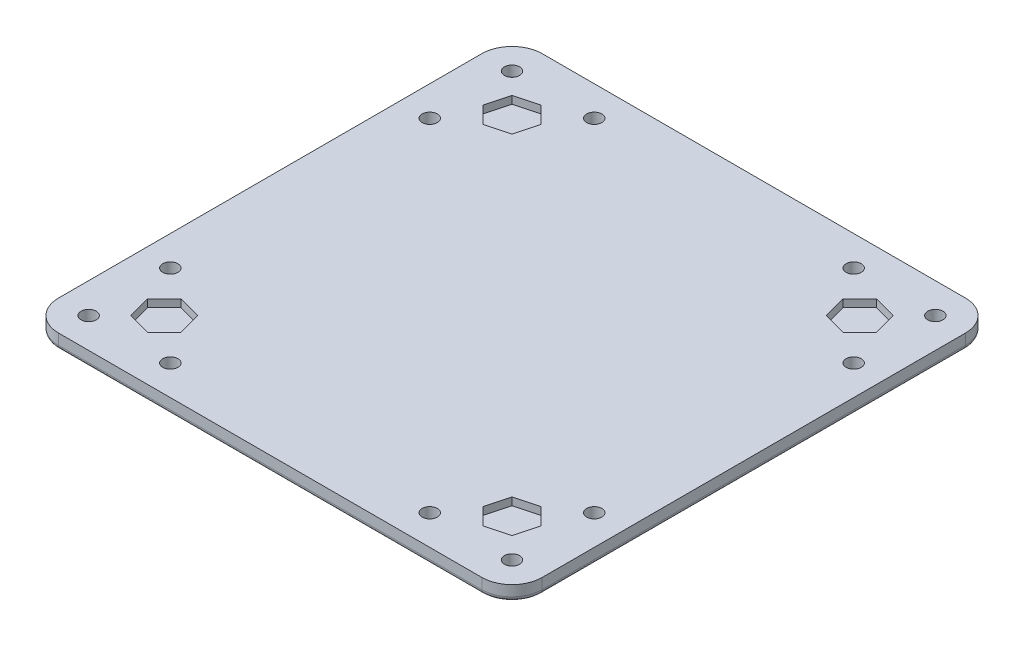
SolidWorks part; units mm, degrees
ref_plane "Front Plane" through (0, 0, 0) normal (0, 0, 1) x (1, 0, 0)
ref_plane "Top Plane" through (0, 0, 0) normal (0, 1, 0) x (1, 0, 0)
ref_plane "Right Plane" through (0, 0, 0) normal (1, 0, 0) x (0, 0, -1)
sketch "Sketch1" plane through (0, 0, 0) normal (0, 1, 0) x (1, 0, 0)
  line L1 (0, 0) -> (203.2, 0)
  line L2 (0, 0) -> (0, 203.2)
  line L3 (0, 203.2) -> (203.2, 203.2)
  line L4 (203.2, 0) -> (203.2, 203.2)
  dimension "D1" = 203.2
  dimension "D2" = 203.2
extrude "Boss-Extrude1" add sketch "Sketch1" along normal blind 6.35
fillet "Fillet1" radius 12.7 4 edges at (0, 3.175, -203.2) (0, 3.175, 0) (203.2, 3.175, 0) (203.2, 3.175, -203.2)
sketch "Sketch2" plane through (0, 0, 0) normal (0, -1, 0) x (1, 0, 0)
  circle A0 centre (12.7, -12.7) radius 3.175
  circle A1 centre (190.5, -12.7) radius 3.175
  circle A2 centre (190.5, -190.5) radius 3.175
  circle A3 centre (12.7, -190.5) radius 3.175
  arc A4 (190.5, -203.2) -> (203.2, -190.5) centre (190.5, -190.5) ccw construction
  arc A5 (12.7, 0) -> (0, -12.7) centre (12.7, -12.7) ccw construction
  dimension "D1" = 6.35
extrude "Cut-Extrude1" cut sketch "Sketch2" against normal through all
sketch "Sketch22" plane through (0, 6.35, 0) normal (0, 1, 0) x (1, 0, 0)
  line L17 (190.5, 203.2) -> (12.7, 203.2) construction
  line L18 (203.2, 12.7) -> (203.2, 190.5) construction
  line L21 (181.6542, 181.6542) -> (172.0521, 184.2271)
  line L22 (172.0521, 184.2271) -> (165.0229, 177.1979)
  line L23 (165.0229, 177.1979) -> (167.5958, 167.5958)
  line L24 (167.5958, 167.5958) -> (177.1979, 165.0229)
  line L25 (177.1979, 165.0229) -> (184.2271, 172.0521)
  line L26 (184.2271, 172.0521) -> (181.6542, 181.6542)
  line L27 (174.625, 174.625) -> (190.5, 190.5) construction
  line L28 (101.6, 203.2) -> (101.6, 0) construction
  line L29 (12.7, 0) -> (190.5, 0) construction
  line L30 (203.2, 101.6) -> (0, 101.6) construction
  line L31 (0, 190.5) -> (0, 12.7) construction
  line L32 (28.575, 174.625) -> (12.7, 190.5) construction
  line L33 (18.9729, 172.0521) -> (21.5458, 181.6542)
  line L34 (26.0021, 165.0229) -> (18.9729, 172.0521)
  line L35 (35.6042, 167.5958) -> (26.0021, 165.0229)
  line L36 (38.1771, 177.1979) -> (35.6042, 167.5958)
  line L37 (31.1479, 184.2271) -> (38.1771, 177.1979)
  line L38 (21.5458, 181.6542) -> (31.1479, 184.2271)
  line L39 (174.625, 28.575) -> (190.5, 12.7) construction
  line L40 (184.2271, 31.1479) -> (181.6542, 21.5458)
  line L41 (177.1979, 38.1771) -> (184.2271, 31.1479)
  line L42 (167.5958, 35.6042) -> (177.1979, 38.1771)
  line L43 (165.0229, 26.0021) -> (167.5958, 35.6042)
  line L44 (172.0521, 18.9729) -> (165.0229, 26.0021)
  line L45 (181.6542, 21.5458) -> (172.0521, 18.9729)
  line L46 (28.575, 28.575) -> (12.7, 12.7) construction
  line L47 (21.5458, 21.5458) -> (31.1479, 18.9729)
  line L48 (31.1479, 18.9729) -> (38.1771, 26.0021)
  line L49 (38.1771, 26.0021) -> (35.6042, 35.6042)
  line L50 (35.6042, 35.6042) -> (26.0021, 38.1771)
  line L51 (26.0021, 38.1771) -> (18.9729, 31.1479)
  line L52 (18.9729, 31.1479) -> (21.5458, 21.5458)
  circle A0 centre (174.625, 174.625) radius 8.609 construction
  circle A1 centre (28.575, 174.625) radius 8.609 construction
  circle A2 centre (174.625, 28.575) radius 8.609 construction
  circle A3 centre (28.575, 28.575) radius 8.609 construction
  dimension "D5" = 17.218
  dimension "D3" = 28.575
  dimension "D4" = 28.575
extrude "Cut-Extrude2" cut sketch "Sketch22" against normal blind 3.175
fillet "Fillet2" radius 1.905 12 edges at (3.7197, 0, -3.7197) (101.6, 0, 0) (199.4803, 0, -3.7197) (203.2, 0, -101.6) (199.4803, 0, -199.4803) (101.6, 0, -203.2) (3.7197, 0, -199.4803) (0, 0, -101.6) (12.7, 0, -15.875) (190.5, 0, -15.875) (190.5, 0, -193.675) (12.7, 0, -193.675)
sketch "Sketch28" plane through (0, 6.35, 0) normal (0, 1, 0) x (1, 0, 0)
  line L0 (190.5, 203.2) -> (12.7, 203.2) construction
  line L1 (203.2, 12.7) -> (203.2, 190.5) construction
  line L2 (12.7, 0) -> (190.5, 0) construction
  line L4 (0, 190.5) -> (0, 12.7) construction
  circle A0 centre (47.117, 190.627) radius 3.175
  circle A1 centre (156.083, 190.627) radius 3.175
  circle A2 centre (190.627, 156.083) radius 3.175
  circle A3 centre (190.627, 47.117) radius 3.175
  circle A4 centre (156.083, 12.573) radius 3.175
  circle A5 centre (47.117, 12.573) radius 3.175
  circle A6 centre (12.573, 156.083) radius 3.175
  circle A7 centre (12.573, 47.117) radius 3.175
  dimension "D4" = 6.35
  dimension "D1" = 12.573
  dimension "D2" = 12.573
  dimension "D3" = 12.573
  dimension "D5" = 12.573
  dimension "D6" = 47.117
  dimension "D7" = 47.117
  dimension "D8" = 47.117
  dimension "D9" = 47.117
extrude "Cut-Extrude3" cut sketch "Sketch28" against normal through all
